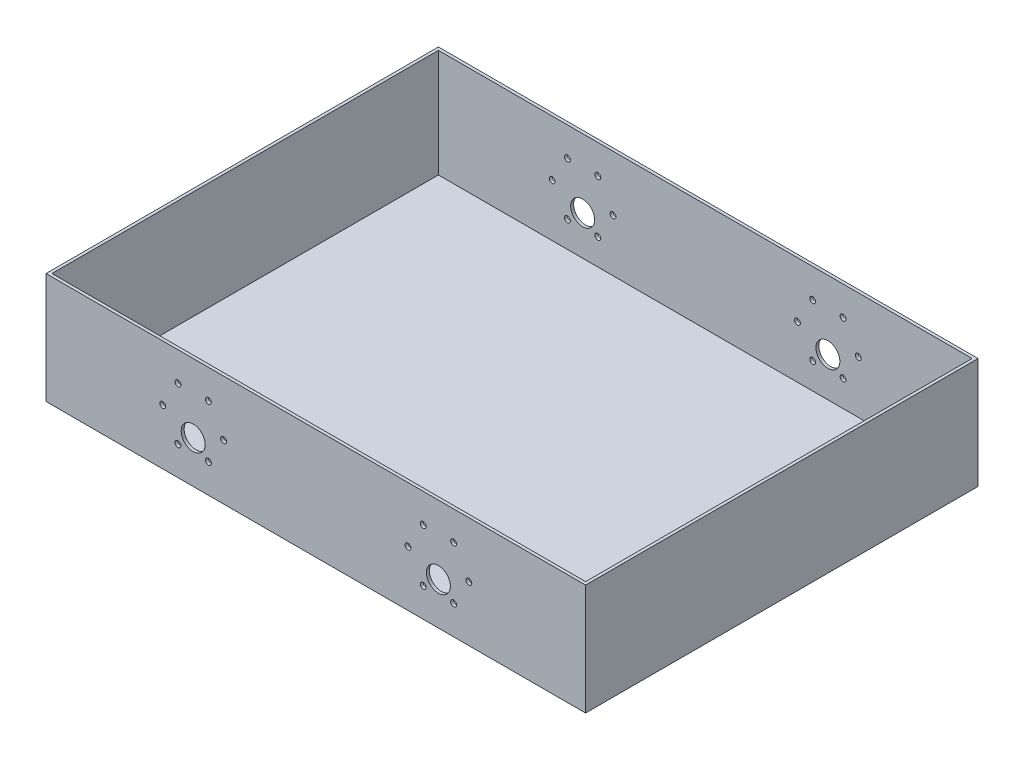
SolidWorks part; units mm, degrees
ref_plane "Front Plane" through (0, 0, 0) normal (0, 0, 1) x (1, 0, 0)
ref_plane "Top Plane" through (0, 0, 0) normal (0, 1, 0) x (1, 0, 0)
ref_plane "Right Plane" through (0, 0, 0) normal (1, 0, 0) x (0, 0, -1)
sketch "Sketch1" plane through (0, 0, 0) normal (0, 1, 0) x (1, 0, 0)
  line L5 (-137.5, -100) -> (137.5, -100)
  line L6 (-137.5, -100) -> (-137.5, 100)
  line L7 (-137.5, 100) -> (137.5, 100)
  line L8 (137.5, -100) -> (137.5, 100)
  line L9 (-137.5, -100) -> (137.5, 100) construction
  line L10 (-137.5, 100) -> (137.5, -100) construction
  point P0 (0, 0)
  dimension "D1" = 275
  dimension "D2" = 200
extrude "Boss-Extrude1" add sketch "Sketch1" along normal blind 1.5
sketch "Sketch3" plane through (0, 1.5, 0) normal (0, 1, 0) x (1, 0, 0)
  line L0 (137.5, 100) -> (-137.5, 100) construction
  line L1 (-136, -98.5) -> (136, -98.5)
  line L2 (-136, -98.5) -> (-136, 98.5)
  line L3 (-136, 98.5) -> (136, 98.5)
  line L4 (136, -98.5) -> (136, 98.5)
  line L7 (-137.5, 100) -> (-137.5, -100) construction
  line L8 (137.5, -100) -> (137.5, 100) construction
  line L9 (-137.5, -100) -> (137.5, -100) construction
  line L10 (137.5, 100) -> (-137.5, 100)
  line L11 (-137.5, 100) -> (-137.5, -100)
  line L12 (137.5, -100) -> (137.5, 100)
  line L13 (-137.5, -100) -> (137.5, -100)
  point P0 (0, 0)
  dimension "D1" = 1.5
  dimension "D2" = 1.5
  dimension "D3" = 1.5
  dimension "D4" = 1.5
extrude "Boss-Extrude2" add sketch "Sketch3" along normal blind 55
sketch "Sketch4" plane through (0, 0, -100) normal (0, 0, -1) x (-1, 0, 0)
  line L0 (0, 0) -> (0, 56.5) construction
  line L1 (-137.5, 0) -> (137.5, 0) construction
  line L2 (-137.5, 56.5) -> (137.5, 56.5) construction
  line L3 (-137.5, 28.25) -> (137.5, 28.25) construction
  line L4 (-137.5, 56.5) -> (-137.5, 0) construction
  line L5 (137.5, 56.5) -> (137.5, 0) construction
  circle A0 centre (-62.5, 28.25) radius 18.5
  circle A2 centre (62.5, 28.25) radius 18.35
  circle A3 centre (-47, 28.25) radius 1.5
  circle A4 centre (-54.75, 14.8266) radius 1.5
  circle A5 centre (-70.25, 14.8266) radius 1.5
  circle A6 centre (-78, 28.25) radius 1.5
  circle A7 centre (-70.25, 41.6734) radius 1.5
  circle A8 centre (-54.75, 41.6734) radius 1.5
  circle A9 centre (78, 28.25) radius 1.5
  circle A10 centre (70.25, 14.8266) radius 1.5
  circle A11 centre (54.75, 14.8266) radius 1.5
  circle A12 centre (47, 28.25) radius 1.5
  circle A13 centre (54.75, 41.6734) radius 1.5
  circle A14 centre (70.25, 41.6734) radius 1.5
  circle A16 centre (-62.5, 21.5) radius 6.1
  circle A17 centre (62.5, 21.5) radius 6.1
  point P31 (-62.5, 28.25)
  point P43 (62.5, 28.25)
  dimension "D1" = 75
  dimension "D2" = 36.7
  dimension "18.35*2" = 37
  dimension "D5" = 3
  dimension "D8" = 3
  dimension "D12" = 12.2
  dimension "D3" = 125
  dimension "D4" = 75
  dimension "D6" = 15.5
  dimension "D9" = 15.5
  dimension "D7" = 6
  dimension "D10" = 6
extrude "MOUNT HOLE" cut sketch "Sketch4" against normal blind 250 contours A8 | A7 | A6 | A4 | A5 | A14 | A13 | A12 | A11 | A10 | A9 | A3 | A16 | A17
